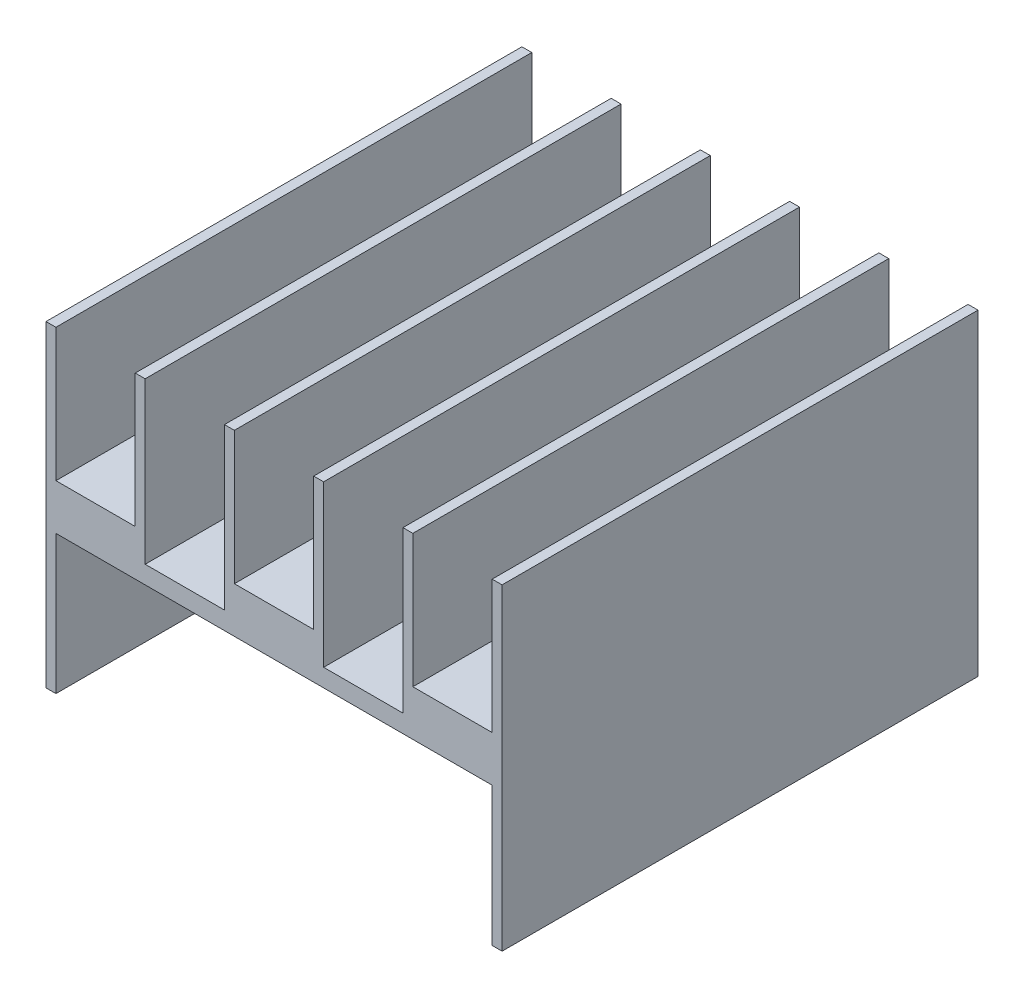
SolidWorks part; units mm, degrees
ref_plane "Front Plane" through (0, 0, 0) normal (0, 0, 1) x (1, 0, 0)
ref_plane "Top Plane" through (0, 0, 0) normal (0, 1, 0) x (1, 0, 0)
ref_plane "Right Plane" through (0, 0, 0) normal (1, 0, 0) x (0, 0, -1)
sketch "Sketch1" plane through (0, 0, 0) normal (0, 0, 1) x (1, 0, 0)
  line L0 (-11, -1) -> (11, -1)
  line L1 (-6.5, 8) -> (-7, 8)
  line L2 (11.5, 8) -> (11.5, -8)
  line L3 (11.5, -8) -> (11, -8)
  line L4 (-11.5, 8) -> (-11.5, -8)
  line L5 (11.5, 8) -> (-11.5, -8) construction
  line L6 (11.5, -8) -> (-11.5, 8) construction
  line L7 (-11, 8) -> (-11, 1.3)
  line L8 (-11, 1.3) -> (-7, 1.3)
  line L9 (-7, 1.3) -> (-7, 8)
  line L10 (-6.5, 8) -> (-6.5, -0.1)
  line L11 (-6.5, -0.1) -> (-2.5, -0.1)
  line L12 (-2.5, -0.1) -> (-2.5, 8)
  line L13 (-11, 8) -> (-11.5, 8)
  line L14 (-2, 8) -> (-2.5, 8)
  line L15 (-2, 8) -> (-2, 1.3)
  line L16 (2, 1.3) -> (2, 8)
  line L17 (2.5, 8) -> (2, 8)
  line L18 (2.5, 8) -> (2.5, -0.1)
  line L19 (6.5, -0.1) -> (6.5, 8)
  line L20 (-2, 1.3) -> (2, 1.3)
  line L21 (2.5, -0.1) -> (6.5, -0.1)
  line L22 (6.5, 8) -> (7, 8)
  line L23 (7, 8) -> (7, 1.3)
  line L24 (7, 1.3) -> (11, 1.3)
  line L25 (11, 1.3) -> (11, 8)
  line L26 (11, 8) -> (11.5, 8)
  line L27 (-11, -1) -> (-11, -8)
  line L28 (11, -1) -> (11, -8)
  line L29 (-11, -8) -> (-11.5, -8)
  point P0 (0, 0)
  dimension "D1" = 23
  dimension "D2" = 16
  dimension "D3" = 9
  dimension "D4" = 6.7
  dimension "D5" = 4
  dimension "D6" = 4
  dimension "D7" = 8.1
  dimension "D9" = 0.5
  dimension "D10" = 0.5
  dimension "D11" = 0.5
  dimension "D12" = 0.5
  dimension "D13" = 0.5
  dimension "D14" = 4
  dimension "D8" = 2
extrude "Boss-Extrude1" add sketch "Sketch1" along normal blind 24 contours L29 L27 L0 L28 L3 L2 L26 L25 L24 L23 L22 L19 L21 L18 L17 L16 L20 L15 L14 L12 L11 L10 L1 L9 L8 L7 L13 L4
sketch "Sketch2" plane through (0, -1, 0) normal (0, -1, 0) x (1, 0, 0)
  line L0 (0, 0) -> (0, 6) construction
  circle A0 centre (0, 6) radius 1.5
  dimension "D2" = 3
  dimension "D1" = 6
extrude "Cut-Extrude1" cut sketch "Sketch2" against normal blind 4
thread "Thread1" pitch 0.25 profile "Thread Profile1" start angle 0, offset 0, length 2.3, pitch 0.25, diameter 3
ref_plane "Plane1" through (1.5, -1, 6) normal (0, 0, 1) x (1, 0, 0)
sketch "Thread Profile1" plane through (1.5, -1, 6) normal (0, 0, 1) x (1, 0, 0)
  line L0 (0, 0) -> (0, 0.25) construction
  line L1 (0, 0) -> (0.1353, 0.0781)
  line L2 (0.1353, 0.0781) -> (0.1353, 0.1094)
  line L3 (0.1353, 0.1094) -> (0, 0.1875)
  line L4 (0.1353, 0.0937) -> (0, 0.0937) construction
  line L11 (0, 0) -> (0, 0.1875)
  point P2 (0, 0)
  dimension "Pitch" = 0.25
  dimension "Profile_Angle" = 60
  dimension "Profile_Land" = 0.0312
  dimension "Profile_Height" = 0.1353
